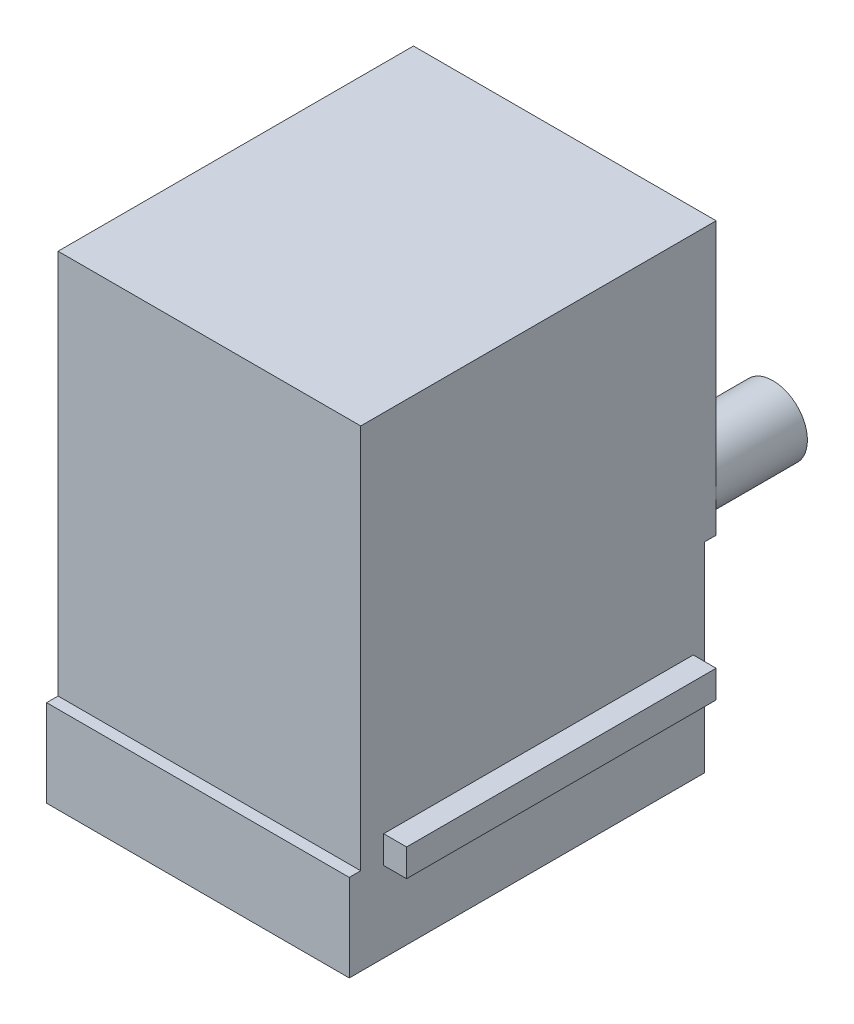
SolidWorks part; units mm, degrees
ref_plane "Front Plane" through (0, 0, 0) normal (0, 0, 1) x (1, 0, 0)
ref_plane "Top Plane" through (0, 0, 0) normal (0, 1, 0) x (1, 0, 0)
ref_plane "Right Plane" through (0, 0, 0) normal (1, 0, 0) x (0, 0, -1)
sketch "Sketch1" plane through (0, 0, 0) normal (0, 0, 1) x (1, 0, 0)
  line L1 (6.6, -10.3) -> (-6.6, -10.3)
  line L2 (6.6, -10.3) -> (6.6, 10.3)
  line L3 (6.6, 10.3) -> (-6.6, 10.3)
  line L4 (-6.6, -10.3) -> (-6.6, 10.3)
  line L5 (6.6, -10.3) -> (-6.6, 10.3) construction
  line L6 (6.6, 10.3) -> (-6.6, -10.3) construction
  point P0 (0, 0)
  dimension "D1" = 13.2
  dimension "D2" = 20.6
extrude "Boss-Extrude1" add sketch "Sketch1" along normal blind 15.5
sketch "Sketch2" plane through (0, 0, 0) normal (0, 0, -1) x (-1, 0, 0)
  line L0 (6.6, -10.3) -> (-6.6, -10.3) construction
  line L2 (6.6, 10.3) -> (6.6, -10.3) construction
  circle A0 centre (5.08, 0) radius 1.5
  circle A1 centre (-5.08, 0) radius 1.5
  point P6 (0, 0)
  point P7 (0, 0)
  dimension "D3" = 3
  dimension "D4" = 3
  dimension "D1" = 10.3
  dimension "D2" = 10.3
  dimension "D5" = 10.16
  dimension "D6" = 1.52
extrude "Boss-Extrude2" add sketch "Sketch2" along normal blind 4
sketch "Sketch3" plane through (0, 0, 15.5) normal (0, 0, 1) x (1, 0, 0)
  line L0 (6.6, -10.3) -> (6.6, 10.3) construction
  line L1 (-6.6, -10.3) -> (6.6, -10.3)
  line L2 (-6.6, -10.3) -> (-6.6, -6.5)
  line L3 (-6.6, -6.5) -> (6.6, -6.5)
  line L4 (6.6, -10.3) -> (6.6, -6.5)
  dimension "D1" = 3.8
extrude "Boss-Extrude3" add sketch "Sketch3" along normal blind 0.5
sketch "Sketch4" plane through (0, -10.3, 0) normal (0, -1, 0) x (1, 0, 0)
  line L0 (-6.6, 16) -> (6.6, 16) construction
  line L1 (-3.6, 15) -> (3.6, 15)
  line L2 (-3.6, 15) -> (-3.6, 13)
  line L3 (-3.6, 4) -> (3.6, 4)
  line L4 (3.6, 15) -> (3.6, 13)
  line L5 (3.6, 13) -> (4.6, 13)
  line L7 (3.6, 6.1) -> (4.6, 6.1)
  line L8 (4.6, 13) -> (4.6, 11)
  line L9 (4.6, 11) -> (5.6, 11)
  line L11 (4.6, 8.4) -> (5.6, 8.4)
  line L12 (5.6, 11) -> (5.6, 8.4)
  line L13 (-3.6, 13) -> (-4.6, 13)
  line L15 (-3.6, 6.1) -> (-4.6, 6.1)
  line L16 (-4.6, 13) -> (-4.6, 11)
  line L17 (-4.6, 11) -> (-5.6, 11)
  line L19 (-4.6, 8.4) -> (-5.6, 8.4)
  line L20 (-5.6, 11) -> (-5.6, 8.4)
  line L21 (-6.6, 16) -> (-6.6, 0) construction
  line L22 (-3.6, 6.1) -> (-3.6, 4)
  line L23 (-4.6, 8.4) -> (-4.6, 6.1)
  line L24 (3.6, 6.1) -> (3.6, 4)
  line L25 (4.6, 8.4) -> (4.6, 6.1)
  dimension "D1" = 11
  dimension "D2" = 1
  dimension "D3" = 6.9
  dimension "D4" = 2
  dimension "D5" = 6.9
  dimension "D6" = 2
  dimension "D7" = 2.6
  dimension "D8" = 2.6
  dimension "D9" = 2
  dimension "D10" = 2
  dimension "D11" = 7.2
  dimension "D12" = 1
  dimension "D13" = 1
  dimension "D14" = 1
  dimension "D15" = 1
  dimension "D16" = 3
extrude "Cut-Extrude1" cut sketch "Sketch4" against normal blind 11
sketch "Sketch5" plane through (0, -10.3, 0) normal (0, -1, 0) x (1, 0, 0)
  line L0 (-3.6, 4) -> (3.6, 4) construction
  line L1 (-2, 4) -> (2.1, 4)
  line L2 (-2, 4) -> (-2, 1.8)
  line L3 (-2, 1.8) -> (2.1, 1.8)
  line L4 (2.1, 4) -> (2.1, 1.8)
  line L5 (3.6, 4) -> (3.6, 6.1) construction
  dimension "D1" = 4.1
  dimension "D2" = 1.5
  dimension "D3" = 2.2
extrude "Cut-Extrude2" cut sketch "Sketch5" against normal blind 5
sketch "Sketch6" plane through (-6.6, 0, 0) normal (-1, 0, 0) x (0, 0, 1)
  line L0 (15.5, 10.3) -> (15.5, -6.5) construction
  line L1 (14.5, -8) -> (1, -8)
  line L2 (14.5, -8) -> (14.5, -6.8)
  line L3 (14.5, -6.8) -> (1, -6.8)
  line L4 (1, -8) -> (1, -6.8)
  line L5 (0, 10.3) -> (0, -10.3) construction
  line L6 (16, -10.3) -> (0, -10.3) construction
  dimension "D1" = 1
  dimension "D2" = 1
  dimension "D3" = 1.2
  dimension "D4" = 3.5
extrude "Boss-Extrude5" add sketch "Sketch6" along normal blind 1
sketch "Sketch7" plane through (6.6, 0, 0) normal (1, 0, 0) x (0, 0, -1)
  line L0 (0, -10.3) -> (0, 10.3) construction
  line L1 (-14.5, -6.8) -> (-1, -6.8)
  line L2 (-14.5, -6.8) -> (-14.5, -5.6)
  line L3 (-14.5, -5.6) -> (-1, -5.6)
  line L4 (-1, -6.8) -> (-1, -5.6)
  line L5 (-15.5, -6.5) -> (-15.5, 10.3) construction
  line L6 (-16, -10.3) -> (0, -10.3) construction
  dimension "D1" = 1.2
  dimension "D2" = 1
  dimension "D3" = 1
  dimension "D4" = 3.5
extrude "Boss-Extrude6" add sketch "Sketch7" along normal blind 1
sketch "Sketch8" plane through (0, 0, 0) normal (0, 0, -1) x (-1, 0, 0)
  line L0 (6.6, 10.3) -> (6.6, -10.3) construction
  line L1 (-6.6, -10.3) -> (6.6, -10.3)
  line L2 (-6.6, -10.3) -> (-6.6, -1.5777)
  line L3 (-6.6, -1.5777) -> (6.6, -1.5777)
  line L4 (6.6, -10.3) -> (6.6, -1.5777)
extrude "Cut-Extrude3" cut sketch "Sketch8" against normal blind 0.5
